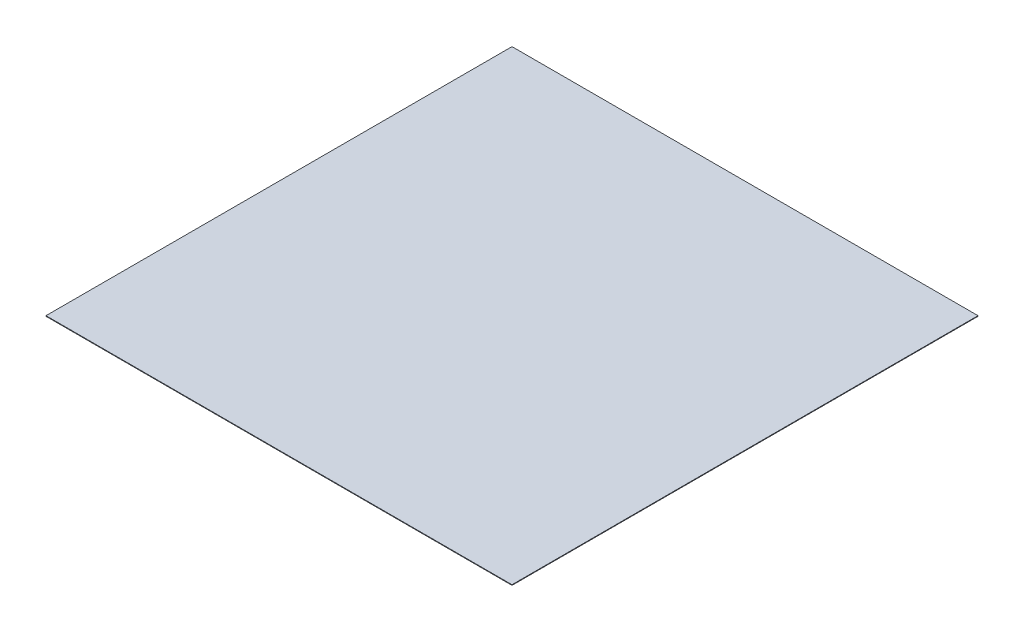
SolidWorks part; units mm, degrees
ref_plane "Front Plane" through (0, 0, 0) normal (0, 0, 1) x (1, 0, 0)
ref_plane "Top Plane" through (0, 0, 0) normal (0, 1, 0) x (1, 0, 0)
ref_plane "Right Plane" through (0, 0, 0) normal (1, 0, 0) x (0, 0, -1)
sketch "Sketch1" plane through (0, 0, 0) normal (0, 1, 0) x (1, 0, 0)
  line L1 (-43023.622, 47496.063) -> (36976.378, 47496.063)
  line L2 (-43023.622, 47496.063) -> (-43023.622, -32503.937)
  line L3 (-43023.622, -32503.937) -> (36976.378, -32503.937)
  line L4 (36976.378, 47496.063) -> (36976.378, -32503.937)
  dimension "D1" = 80000
  dimension "D2" = 80000
extrude "Boss-Extrude1" add sketch "Sketch1" along normal mid plane 100
